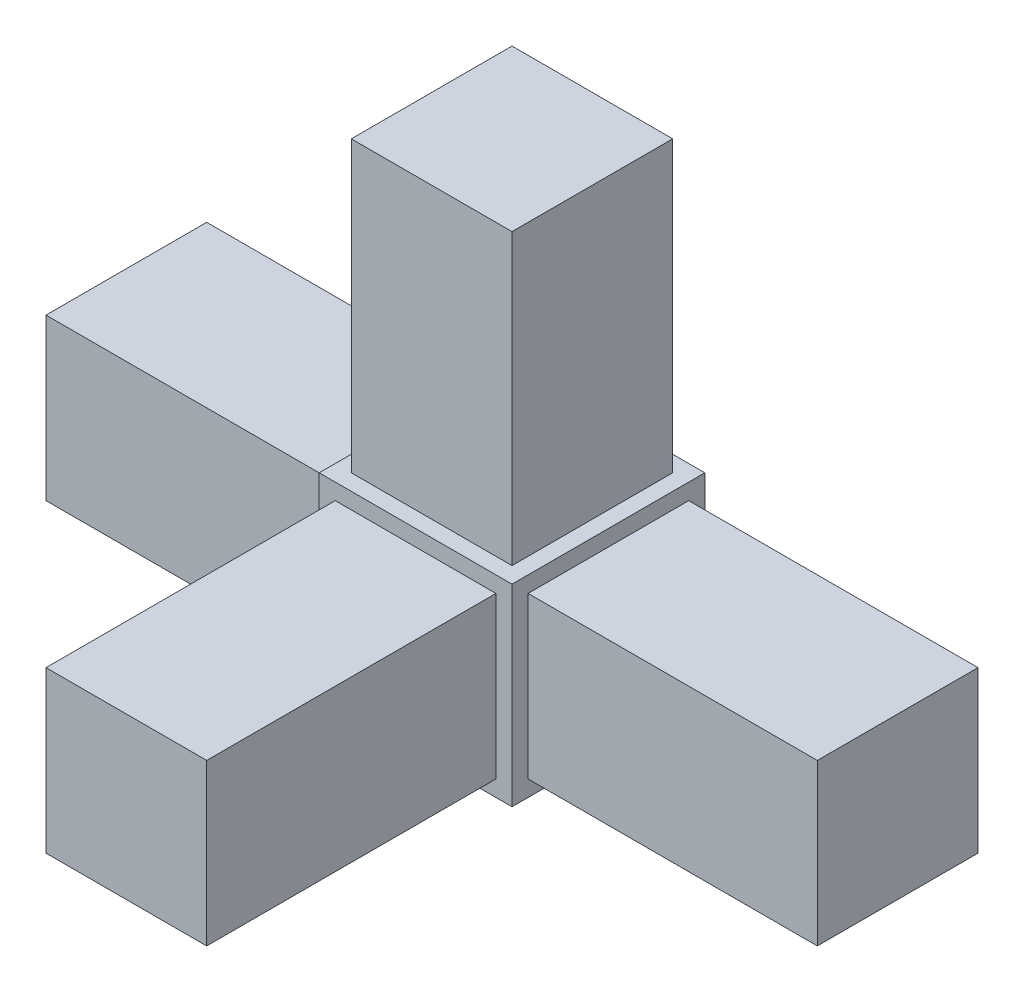
SolidWorks part; units mm, degrees
material "ABS"
ref_plane "Front Plane" through (0, 0, 0) normal (0, 0, 1) x (1, 0, 0)
ref_plane "Top Plane" through (0, 0, 0) normal (0, 1, 0) x (1, 0, 0)
ref_plane "Right Plane" through (0, 0, 0) normal (1, 0, 0) x (0, 0, -1)
sketch "Sketch1" plane through (0, 0, 0) normal (0, 0, 1) x (1, 0, 0)
  line L1 (9.525, -9.525) -> (-9.525, -9.525)
  line L2 (9.525, -9.525) -> (9.525, 9.525)
  line L3 (9.525, 9.525) -> (-9.525, 9.525)
  line L4 (-9.525, -9.525) -> (-9.525, 9.525)
  line L5 (9.525, -9.525) -> (-9.525, 9.525) construction
  line L6 (9.525, 9.525) -> (-9.525, -9.525) construction
  point P0 (0, 0)
  dimension "D1" = 19.05
extrude "Boss-Extrude1" add sketch "Sketch1" along normal blind 19.05
sketch "Sketch2" plane through (0, 9.525, 0) normal (0, 1, 0) x (1, 0, 0)
  line L0 (-9.525, 0) -> (9.525, -19.05) construction
  line L2 (-7.9375, -1.5875) -> (7.9375, -1.5875)
  line L3 (-7.9375, -1.5875) -> (-7.9375, -17.4625)
  line L4 (-7.9375, -17.4625) -> (7.9375, -17.4625)
  line L5 (7.9375, -1.5875) -> (7.9375, -17.4625)
  line L6 (-7.9375, -1.5875) -> (7.9375, -17.4625) construction
  line L7 (-7.9375, -17.4625) -> (7.9375, -1.5875) construction
  point P4 (0, -9.525)
  dimension "D1" = 15.875
extrude "Boss-Extrude2" add sketch "Sketch2" along normal blind 28.575
sketch "Sketch3" plane through (9.525, 0, 0) normal (1, 0, 0) x (0, 0, -1)
  line L0 (-19.05, 9.525) -> (0, -9.525) construction
  line L2 (-17.4625, -7.9375) -> (-1.5875, -7.9375)
  line L3 (-17.4625, -7.9375) -> (-17.4625, 7.9375)
  line L4 (-17.4625, 7.9375) -> (-1.5875, 7.9375)
  line L5 (-1.5875, -7.9375) -> (-1.5875, 7.9375)
  line L6 (-17.4625, -7.9375) -> (-1.5875, 7.9375) construction
  line L7 (-17.4625, 7.9375) -> (-1.5875, -7.9375) construction
  point P4 (-9.525, 0)
  dimension "D1" = 15.875
extrude "Boss-Extrude3" add sketch "Sketch3" along normal blind 28.575
sketch "Sketch4" plane through (0, 0, 19.05) normal (0, 0, 1) x (1, 0, 0)
  line L0 (-9.525, 9.525) -> (9.525, -9.525) construction
  line L2 (7.9375, -7.9375) -> (-7.9375, -7.9375)
  line L3 (7.9375, -7.9375) -> (7.9375, 7.9375)
  line L4 (7.9375, 7.9375) -> (-7.9375, 7.9375)
  line L5 (-7.9375, -7.9375) -> (-7.9375, 7.9375)
  line L6 (7.9375, -7.9375) -> (-7.9375, 7.9375) construction
  line L7 (7.9375, 7.9375) -> (-7.9375, -7.9375) construction
  point P4 (0, 0)
  dimension "D1" = 15.875
extrude "Boss-Extrude4" add sketch "Sketch4" along normal blind 28.575
sketch "Sketch5" plane through (-9.525, 0, 0) normal (-1, 0, 0) x (0, 0, 1)
  line L0 (1.5875, 7.9375) -> (17.4625, 7.9375) construction
  line L1 (1.5875, 7.9375) -> (17.4625, 7.9375)
  line L2 (1.5875, 7.9375) -> (1.5875, -7.9375)
  line L3 (1.5875, -7.9375) -> (17.4625, -7.9375)
  line L4 (17.4625, 7.9375) -> (17.4625, -7.9375)
  line L5 (1.5875, -7.9375) -> (1.5875, 7.9375) construction
  line L6 (9.525, -9.525) -> (9.525, -7.9375) construction
  line L7 (19.05, -9.525) -> (0, -9.525) construction
  line L8 (1.5875, 0) -> (0, 0) construction
extrude "Boss-Extrude5" add sketch "Sketch5" along normal blind 28.575
equation "\"Height\"= 32in"
equation "\"Width\"= 23in"
equation "\"Depth\"= 20in"
equation "\"Plexi\"= .121in"
equation "\"MagnetThickness\"= .125in"
equation "\"MagnetDiameter\"= 12mm"
equation "\"DoorPlexi\"= \"Plexi\""
equation "\"BasePlateThickness\"= 0.5in"
equation "\"BasePlateWidth\"= \"Width\"+\"EBWidth\"-2*\"Plexi\""
equation "\"BasePlateDepth\"= \"TopBarDepth\"+2*\"CornerCube\""
equation "\"Boxsize\"= .75in"
equation "\"Boxinner\"= .625in"
equation "\"CornerCube\"= 0.75in"
equation "\"FingerLength\"= 1.125in"
equation "\"Cutwidth\"= .016in"
equation "\"Earsize\"= 1in + \"Cutwidth\" /2"
equation "\"Slotsize\"= 1in - \"Cutwidth\" / 2"
equation "\"InnerWidth\"= \"Width\" - 2* \"Plexi\""
equation "\"InnerHeight\"= \"Height\" -2 * \"Plexi\""
equation "\"InnerDepth\"= \"Depth\" - 2*\"Plexi\""
equation "\"RearNumHoles\"= 4"
equation "\"RearHolesBorder\"= 2.25"
equation "\"RearHoleSpacing\"= (\"Width\" - 2*\"RearHolesBorder\") / (\"RearNumHoles\"-1)"
equation "\"RearBarLength\"= (\"InnerWidth\"-2*\"CornerCube\")"
equation "\"RearTopNumHoles\"= 4"
equation "\"RearTopHolesBorder\"= 3.1"
equation "\"RearTopHolesSpacing\"= (\"Width\" - 2*\"RearTopHolesBorder\") / (\"RearTopNumHoles\"-1)"
equation "\"SideTopNumHoles\"= 4"
equation "\"SideTopHoleOffset\"=\"CornerCube\"+\"FingerLength\"+\"Plexi\"+.5"
equation "\"SideTopHoleSpacing\"= (\"TopBarDepth\"-2*\"SideTopHoleOffset\") / (\"SideTopNumHoles\"-1)"
equation "\"SideHorizNumHoles\"= 4"
equation "\"SideHorizHoleBorder\"= 1.50"
equation "\"SideHorizHoleSpacing\"= (\"TopBarDepth\"-2*\"SideHorizHoleBorder\") / (\"SideHorizNumHoles\"-1)"
equation "\"SideVertBarLength\"=\"Height\"-\"BasePlateThickness\"-2*\"CornerCube\"-\"Plexi\""
equation "\"SideVertNumHoles\"= 4"
equation "\"SideVertHolesBorder\"= \"CornerCube\"+\"FingerLength\"+1.50"
equation "\"SideVertHoleSpacing\"= (\"InnerHeight\" - 2*\"SideVertHolesBorder\") / (\"SideVertNumHoles\"-1)"
equation "\"RearSideVertNumHoles\"= 4"
equation "\"RearSideVertHolesBorder\"= 2.4"
equation "\"RearSideVertHoleSpacing\"= (\"InnerHeight\" - 2*\"RearSideVertHolesBorder\") / (\"RearSideVertNumHoles\"-1)"
equation "\"RivetDia\"= .228in"
equation "\"SlotDepth\"= \"Plexi\" + 0.75in + .005in"
equation "\"SideSlotWidth\"= \"Plexi\"+.005in"
equation "\"SidePanelVertSpacing\"= (\"Height\"-2*(1.75-\"Plexi\")) / 5"
equation "\"BottomPanelSideHoleSpacing\"= (\"InnerDepth\"-2*(1.75-\"Plexi\")) / 4"
equation "\"FrontDoorGap\"= .1in"
equation "\"TopDepth\"= \"Depth\"-\"DoorPlexi\"-\"FrontDoorGap\""
equation "\"TopBarDepth\"= \"Depth\"-\"DoorPlexi\"-\"Plexi\"-2*\"MagnetThickness\"-2*\"CornerCube\""
equation "\"D1@Boss-Extrude1\"=\"CornerCube\""
equation "\"D1@Sketch1\"=\"CornerCube\""
equation "\"D1@Boss-Extrude4\"=\"FingerLength\""
equation "\"D1@Boss-Extrude3\"=\"FingerLength\""
equation "\"D1@Boss-Extrude2\"=\"FingerLength\""
equation "\"D1@Boss-Extrude5\"=\"FingerLength\""
equation "\"D1@Sketch2\"=\"Boxinner\""
equation "\"D1@Sketch4\"=\"Boxinner\""
equation "\"D1@Sketch3\"=\"Boxinner\""
